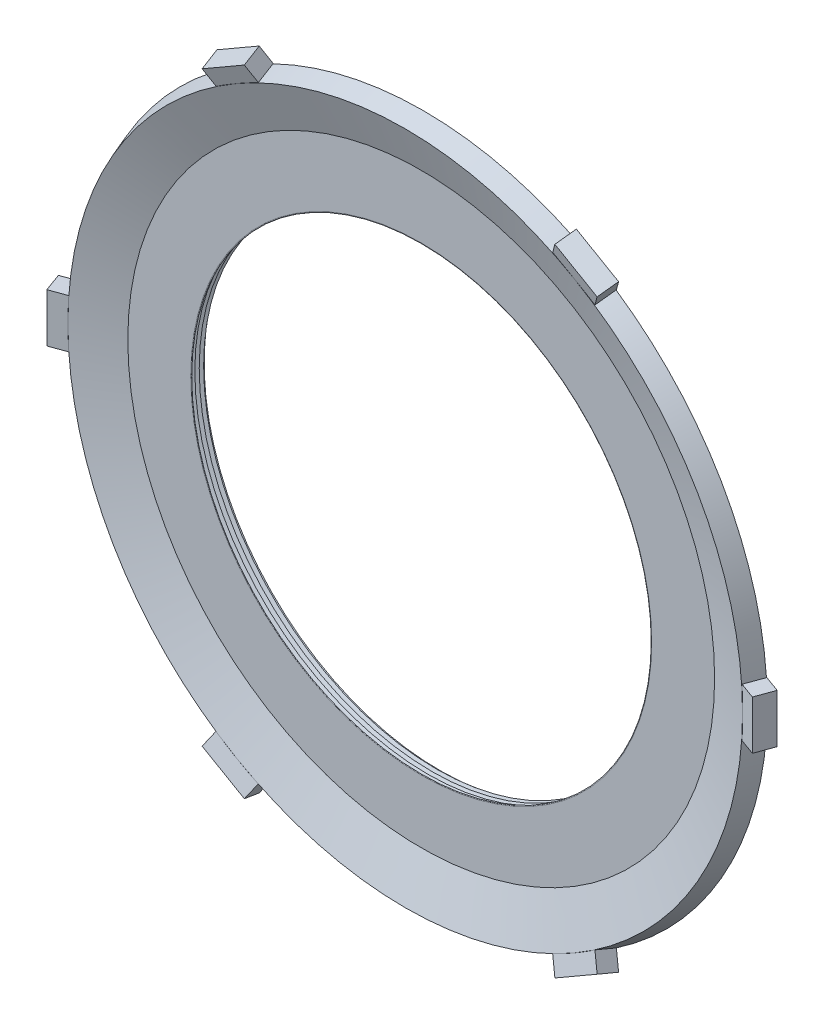
SolidWorks part; units mm, degrees
ref_plane "Front Plane" through (0, 0, 0) normal (0, 0, 1) x (1, 0, 0)
ref_plane "Top Plane" through (0, 0, 0) normal (0, 1, 0) x (1, 0, 0)
ref_plane "Right Plane" through (0, 0, 0) normal (1, 0, 0) x (0, 0, -1)
sketch "Sketch1" plane through (0, 0, 0) normal (0, 1, 0) x (1, 0, 0)
  line L0 (0, 37.8381) -> (0, -37.4672) construction
  line L1 (23.876, 2.032) -> (31.242, 2.032)
  line L2 (31.242, 2.032) -> (35.814, 0.3679)
  line L3 (35.814, 0.3679) -> (35.1254, -1.524)
  line L4 (35.1254, -1.524) -> (30.5534, 0.1401)
  line L5 (30.5534, 0.1401) -> (23.876, 0.1401)
  line L6 (23.876, 0.1401) -> (23.876, 2.032)
  dimension "D1" = 3.556
  dimension "G/2" = 2.032
  dimension "D4" = 20
  dimension "D5" = 4.572
  dimension "D6" = 35.814
  dimension "TS" = 47.752
revolve "Revolve1" add sketch "Sketch1" angle 360 about L0
sketch "Sketch3" plane through (0, 0, 0) normal (0, 1, 0) x (1, 0, 0)
  line L0 (34.798, 0.7377) -> (37.4235, -0.2179)
  line L1 (35.814, 0.3679) -> (31.242, 2.032) construction
  line L2 (37.4235, -0.2179) -> (36.7349, -2.1098)
  line L3 (36.7349, -2.1098) -> (34.1094, -1.1542)
  line L4 (35.1254, -1.524) -> (30.5534, 0.1401) construction
  line L5 (34.1094, -1.1542) -> (34.798, 0.7377)
  dimension "D1" = 34.798
  dimension "D2" = 2.794
extrude "Extrude3" add sketch "Sketch3" along normal blind 2.54 and the other way blind 2.54
pattern_circular "CirPattern1" count 6 over 360 about axis through (0, 0, 0) along (0, 0, 1) of "Extrude3"
fillet "Fillet4" radius 0.127 2 edges at (-23.876, 0, -2.032) (-23.876, 0, -0.1401)
sketch "Sketch4" plane through (0, 0, 0) normal (0, 1, 0) x (1, 0, 0)
  line L0 (-23.876, 0.1401) -> (-23.876, 1.02)
  line L2 (-23.876, 1.02) -> (-24.638, 0.58)
  line L3 (-24.638, 0.58) -> (-23.876, 0.1401)
  line L4 (-30.5534, 0.1401) -> (30.5534, 0.1401) construction
  line L5 (-23.876, 1.905) -> (-23.876, 0.2671) construction
  dimension "D1" = 60
  dimension "D2" = 60
  dimension "D3" = 0.762
revolve "Cut-Revolve1" cut sketch "Sketch4" angle 360 about axis through (0, 0, -37.8381) along (0, 0, 1)
pattern_linear "LPattern1" count 5 spacing 0.4572 along (0, 0, -1) of "Cut-Revolve1"
